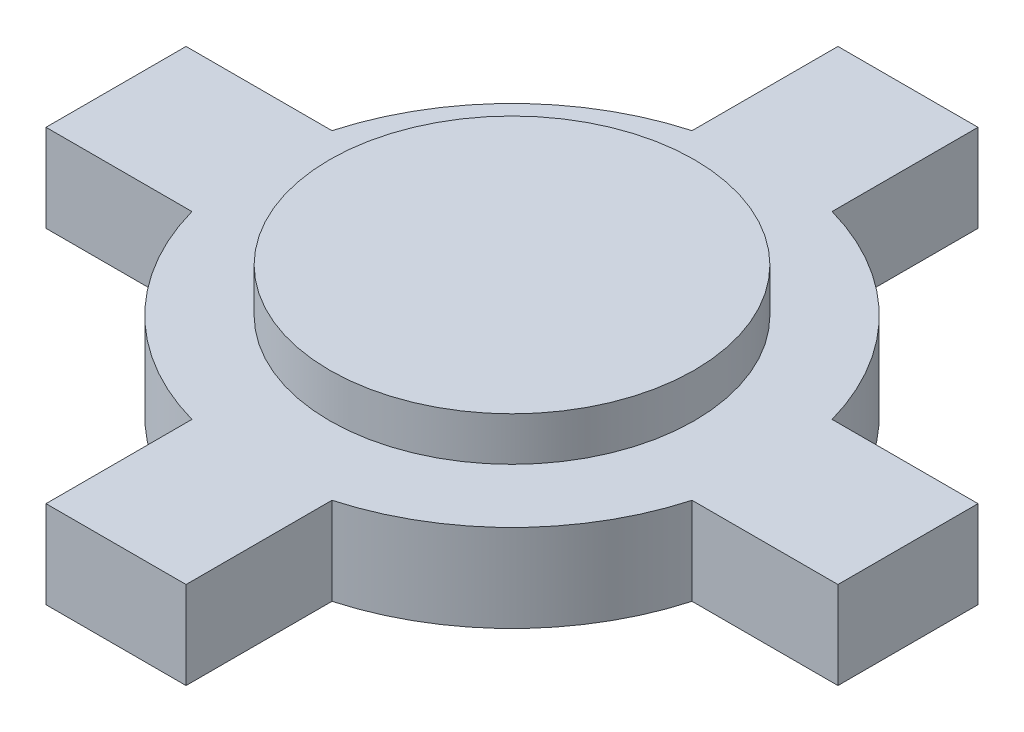
SolidWorks part; units mm, degrees
ref_plane "前视基准面" through (0, 0, 0) normal (0, 0, 1) x (1, 0, 0)
ref_plane "上视基准面" through (0, 0, 0) normal (0, 1, 0) x (1, 0, 0)
ref_plane "右视基准面" through (0, 0, 0) normal (1, 0, 0) x (0, 0, -1)
other "Configuration Table"
sketch "草图1" plane through (0, 0, 0) normal (0, 1, 0) x (1, 0, 0)
  line L0 (0, 7.9747) -> (0, -8.6444) construction
  line L1 (-13.5703, 2.4) -> (-8.5703, 2.4)
  line L2 (-13.5703, 2.4) -> (-13.5703, -2.4)
  line L3 (-13.5703, -2.4) -> (-8.5703, -2.4)
  line L4 (13.5703, 2.4) -> (13.5703, -2.4)
  line L5 (-2.4, 13.5703) -> (2.4, 13.5703)
  line L6 (-2.4, 13.5703) -> (-2.4, 8.5703)
  line L7 (-2.4, -13.5703) -> (2.4, -13.5703)
  line L8 (2.4, 13.5703) -> (2.4, 8.5703)
  line L13 (-10.8789, 0) -> (11.1113, 0) construction
  line L15 (-2.4, -8.5703) -> (-2.4, -13.5703)
  line L16 (8.5703, 2.4) -> (13.5703, 2.4)
  line L17 (8.5703, -2.4) -> (13.5703, -2.4)
  line L18 (2.4, -8.5703) -> (2.4, -13.5703)
  arc A0 (-2.4, 8.5703) -> (-8.5703, 2.4) centre (0, 0) ccw
  arc A1 (8.5703, 2.4) -> (2.4, 8.5703) centre (0, 0) ccw
  arc A2 (2.4, -8.5703) -> (8.5703, -2.4) centre (0, 0) ccw
  arc A3 (-8.5703, -2.4) -> (-2.4, -8.5703) centre (0, 0) ccw
  dimension "D1" = 17.8
  dimension "D2" = 4.8
  dimension "D3" = 5
extrude "凸台-拉伸1" add sketch "草图1" along normal blind 3
sketch "草图2" plane through (0, 3, 0) normal (0, 1, 0) x (1, 0, 0)
  circle A0 centre (0, 0) radius 6.25
  dimension "D1" = 12.5
extrude "凸台-拉伸2" add sketch "草图2" along normal blind 1.5
